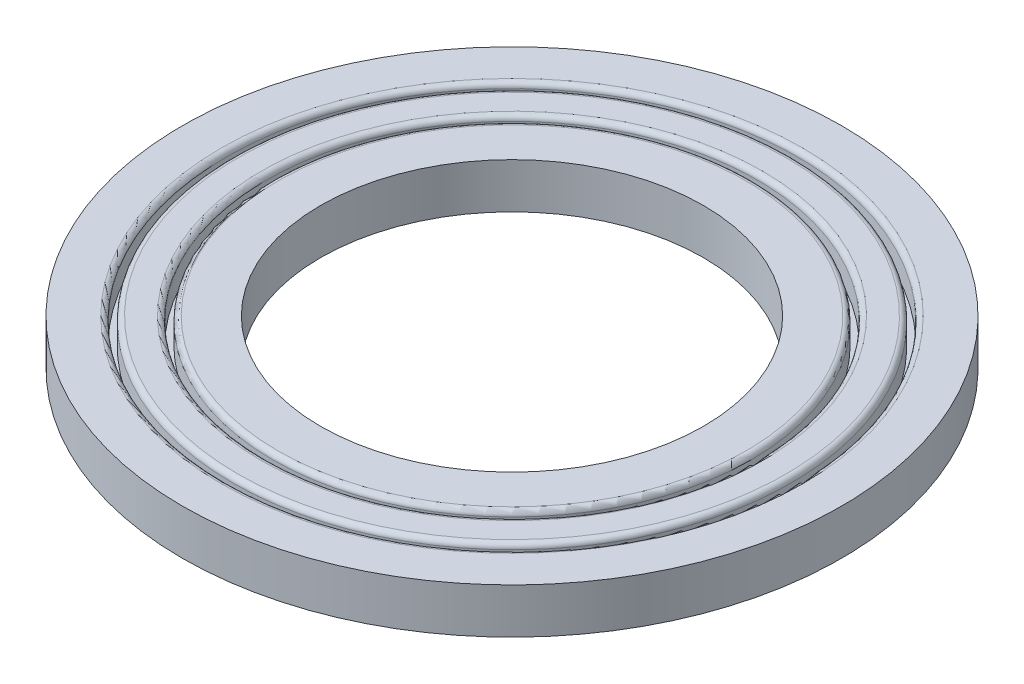
SolidWorks part; units mm, degrees
ref_plane "前视基准面" through (0, 0, 0) normal (0, 0, 1) x (1, 0, 0)
ref_plane "上视基准面" through (0, 0, 0) normal (0, 1, 0) x (1, 0, 0)
ref_plane "右视基准面" through (0, 0, 0) normal (1, 0, 0) x (0, 0, -1)
other "Configuration Table"
sketch "草图1" plane through (0, 0, 0) normal (0, 1, 0) x (1, 0, 0)
  circle A0 centre (0, 0) radius 25.5
extrude "凸台-拉伸1" add sketch "草图1" along normal blind 3.5
sketch "草图2" plane through (0, 3.5, 0) normal (0, 1, 0) x (1, 0, 0)
  circle A0 centre (0, 0) radius 19
  circle A1 centre (0, 0) radius 18.5
  dimension "D1" = 0.5
  dimension "D2" = 37
extrude "切除-拉伸1" cut sketch "草图2" against normal blind 2
sketch "草图3" plane through (0, 3.5, 0) normal (0, 1, 0) x (1, 0, 0)
  circle A0 centre (0, 0) radius 22.1
  circle A1 centre (0, 0) radius 21.6
  dimension "D1" = 0.5
  dimension "D2" = 43.2
extrude "切除-拉伸2" cut sketch "草图3" against normal blind 2
fillet "圆角1" radius 0.4 4 edges at (0, 3.5, 18.5) (0, 3.5, 19) (0, 3.5, 21.6) (0, 3.5, 22.1)
sketch "草图4" plane through (0, 0, 0) normal (0, -1, 0) x (1, 0, 0)
  circle A0 centre (0, 0) radius 14.809
extrude "切除-拉伸3" cut sketch "草图4" against normal blind 10
